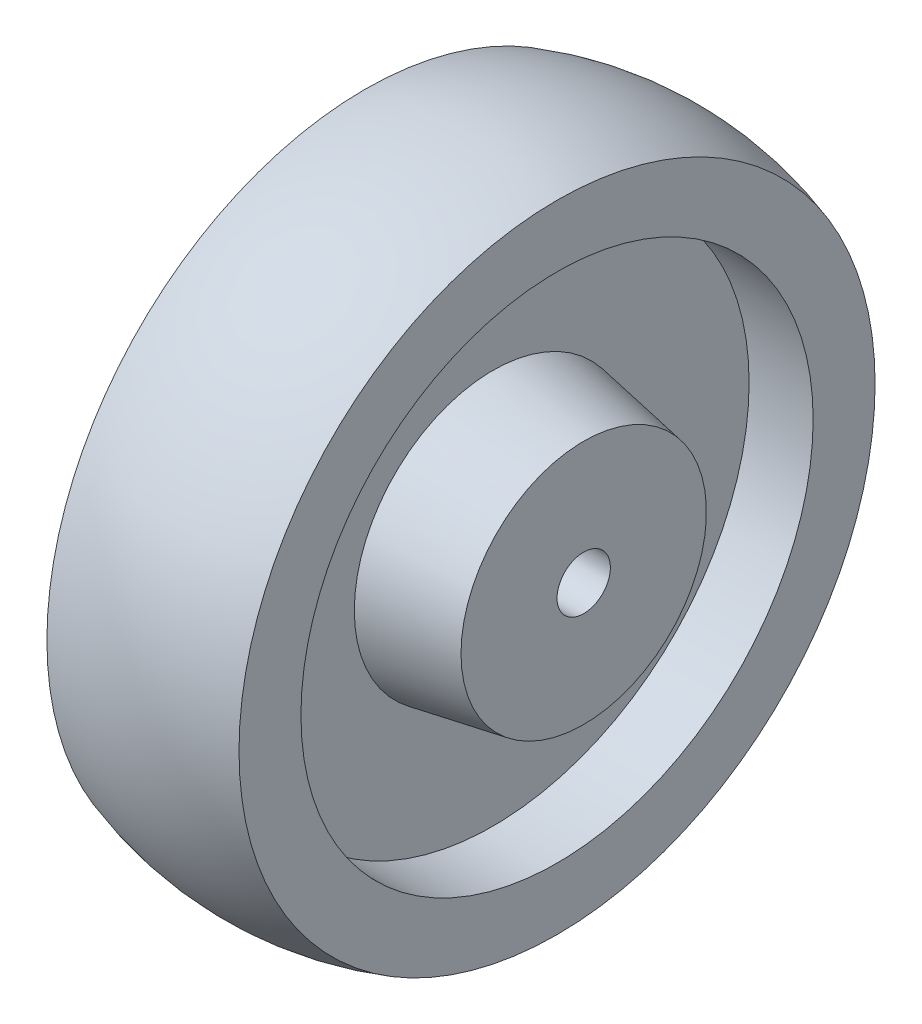
SolidWorks part; units mm, degrees
ref_plane "Front Plane" through (0, 0, 0) normal (0, 0, 1) x (1, 0, 0)
ref_plane "Top Plane" through (0, 0, 0) normal (0, 1, 0) x (1, 0, 0)
ref_plane "Right Plane" through (0, 0, 0) normal (1, 0, 0) x (0, 0, -1)
sketch "Sketch1" plane through (0, 0, 0) normal (0, 0, 1) x (1, 0, 0)
  line L0 (0, 0) -> (0, 62.5) construction
  line L1 (0, 0) -> (23.5429, 0) construction
  line L2 (-23, 5) -> (23, 5)
  line L3 (23, 5) -> (23, 23)
  line L4 (23, 23) -> (6, 26)
  line L5 (6, 26) -> (6, 48)
  line L6 (6, 48) -> (18, 48)
  line L7 (18, 48) -> (18, 59.61)
  line L8 (-23, 5) -> (-23, 23)
  line L9 (-23, 23) -> (-6, 26)
  line L10 (-6, 26) -> (-6, 48)
  line L11 (-6, 48) -> (-18, 48)
  line L12 (-18, 48) -> (-18, 59.61)
  arc A0 (18, 59.61) -> (-18, 59.61) centre (0, 5) ccw
  point P7 (0, 5)
  point P14 (0, 0)
  point P15 (0, 0)
  point P16 (0, 0)
  point P17 (0, 21.2543)
  point P18 (0, 7.6379)
  point P19 (0, 0)
  dimension "D1" = 62.5
  dimension "D2" = 46
  dimension "D3" = 5
  dimension "D4" = 23
  dimension "D5" = 17
  dimension "D6" = 26
  dimension "D7" = 48
  dimension "D8" = 18
revolve "Revolve1" add sketch "Sketch1" angle 360 about L1
